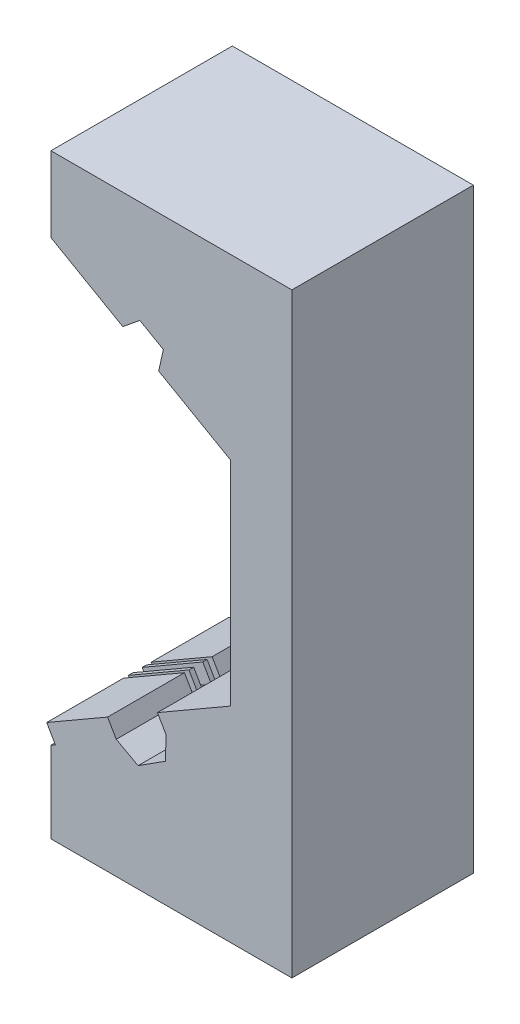
SolidWorks part; units mm, degrees
ref_plane "Front Plane" through (0, 0, 0) normal (0, 0, 1) x (1, 0, 0)
ref_plane "Top Plane" through (0, 0, 0) normal (0, 1, 0) x (1, 0, 0)
ref_plane "Right Plane" through (0, 0, 0) normal (1, 0, 0) x (0, 0, -1)
sketch "Sketch1" plane through (0, 0, 0) normal (0, 0, 1) x (1, 0, 0)
  line L0 (0.7953, -25.456) -> (8.3551, -21.0913)
  line L1 (0.7953, 34.1378) -> (28.6941, 34.1378)
  line L2 (0.7953, 34.1378) -> (0.7953, 25.4267)
  line L3 (0.7953, -34.8515) -> (28.6941, -34.8515)
  line L4 (28.6941, 34.1378) -> (28.6941, -34.8515)
  line L5 (8.3551, -21.0913) -> (10.8905, -22.4625)
  line L6 (10.8905, -22.4625) -> (14.0441, -20.4464)
  line L7 (14.0441, -20.4464) -> (14.1295, -17.7575)
  line L8 (14.1295, -17.7575) -> (22.4796, -12.9365)
  line L11 (22.4796, 13.0123) -> (13.2673, 18.2864)
  line L12 (13.2673, 18.2864) -> (13.8114, 20.7132)
  line L13 (13.8114, 20.7132) -> (11.0901, 22.2712)
  line L14 (11.0901, 22.2712) -> (9.1144, 20.6639)
  line L15 (9.1144, 20.6639) -> (0.7953, 25.4267)
  line L16 (0.7953, -25.456) -> (0.7953, -34.8515)
  line L17 (22.4796, -12.9365) -> (22.4796, -1.5436)
  line L18 (22.4796, -1.5436) -> (23.0165, -1.5436)
  line L20 (24.1482, -0.9477) -> (24.1482, 0.9797)
  line L22 (23.0165, 1.4917) -> (22.4796, 1.4917)
  line L23 (22.4796, 1.4917) -> (22.4796, 13.0123)
  line L24 (0.0371, 25.9047) -> (9.9572, 20.1774) construction
  line L25 (23.0165, -1.5436) -> (23.0165, -1.3275)
  line L26 (23.0165, -1.3275) -> (23.5495, -1.3275)
  line L27 (23.5495, -1.3275) -> (24.1482, -0.9477)
  line L28 (23.0165, 1.4917) -> (23.0165, 1.2788)
  line L29 (23.0165, 1.2788) -> (23.5495, 1.2788)
  line L30 (23.5495, 1.2788) -> (24.1482, 0.9797)
  point P11 (7.6664, 20.3453)
  point P12 (9.1144, 20.6639)
  point P25 (6.6681, 20.9216)
  point P29 (0, 0)
  point P32 (10.8905, 22.1088)
extrude "Boss-Extrude1" add sketch "Sketch1" along normal blind 10 and the other way blind 11
sketch "Sketch2" plane through (22.4796, 0, 0) normal (-1, 0, 0) x (0, 0, 1)
  line L1 (-1.05, -15.5034) -> (-1.55, -15.5034)
  line L2 (-1.05, -15.5034) -> (-1.05, 18.2864)
  line L3 (-1.05, 18.2864) -> (-1.55, 18.2864)
  line L4 (-11, -15.5034) -> (-11, 18.2864)
  line L5 (-2.1, 18.2864) -> (-11, 18.2864)
  line L6 (1.1, 18.2864) -> (10, 18.2864)
  line L7 (0.05, -15.4238) -> (0.55, -15.4238)
  line L8 (0.05, -15.4238) -> (0.05, 18.2864)
  line L9 (0.05, 18.2864) -> (0.55, 18.2864)
  line L10 (10, -15.4238) -> (10, 18.2864)
  line L11 (-1, -12.9523) -> (-1, -1.4976) construction
  line L13 (0.55, -15.4238) -> (0.55, 18.2864)
  line L15 (1.1, -15.4238) -> (1.1, 18.2864)
  line L17 (-1.55, 18.2864) -> (-1.55, -15.5034)
  line L19 (-2.1, 18.2864) -> (-2.1, -15.5034)
  line L20 (0, -12.9523) -> (0, -1.4976) construction
  line L21 (-2.1, -15.5034) -> (-11, -15.5034)
  line L22 (1.1, -15.4238) -> (10, -15.4238)
  dimension "D1" = 0.55
  dimension "D2" = 0.55
  dimension "D3" = 0.05
  dimension "D4" = 0.05
  dimension "D5" = 0.5
  dimension "D6" = 0.5
extrude "Boss-Extrude2" add sketch "Sketch2" along normal blind 0.9
sketch "Sketch4" plane through (21.5796, 0, 0) normal (-1, 0, 0) x (0, 0, 1)
  line L1 (-2.1, 1.4917) -> (1.1, 1.4917)
  line L2 (-2.1, 1.4917) -> (-2.1, -1.5436)
  line L3 (-2.1, -1.5436) -> (1.1, -1.5436)
  line L4 (1.1, 1.4917) -> (1.1, -1.5436)
extrude "Cut-Extrude1" cut sketch "Sketch4" against normal blind 0.9
sketch "Sketch5" plane through (21.5796, 0, 0) normal (-1, 0, 0) x (0, 0, 1)
  line L0 (1.1, 13.5276) -> (1.1, -13.4562) construction
  line L1 (1.1, 2.605) -> (10, 2.605)
  line L2 (1.1, 2.605) -> (1.1, -3.3199)
  line L3 (1.1, -3.3199) -> (10, -3.3199)
  line L4 (10, 2.605) -> (10, -3.3199)
  line L5 (10, -13.4562) -> (10, 13.5276) construction
  line L6 (-11, 13.5276) -> (-11, -13.4562) construction
  line L7 (-11, -4.75) -> (-2.1, -4.75)
  line L8 (-11, -4.75) -> (-11, 3.5097)
  line L9 (-11, 3.5097) -> (-2.1, 3.5097)
  line L10 (-2.1, -4.75) -> (-2.1, 3.5097)
  line L11 (-2.1, -13.4562) -> (-2.1, 13.5276) construction
extrude "Boss-Extrude3" add sketch "Sketch5" against normal blind 3.9
sketch "Sketch6" plane through (11.2216, -19.4364, 0) normal (-0.5, 0.866, 0) x (0.866, 0.5, 0)
  line L0 (-1.4702, 0) -> (-12.9202, 0) construction
  line L1 (13.4092, -10) -> (3.3578, -10)
  line L2 (13.4092, -10) -> (13.4092, -1.1)
  line L3 (13.4092, 11) -> (3.3578, 11)
  line L4 (-11.4513, -10) -> (-11.4513, -1.1)
  line L5 (13.4092, -1.1) -> (3.3578, -1.1)
  line L7 (13.4092, -0.55) -> (3.3855, -0.55)
  line L9 (13.4092, 1.05) -> (3.3855, 1.05)
  line L11 (13.4092, 0) -> (3.3855, 0)
  line L13 (13.4092, 2.1) -> (3.3578, 2.1)
  line L15 (13.4092, 1.55) -> (3.3855, 1.55)
  line L17 (-3.3455, -0.55) -> (-3.3455, 0)
  line L18 (3.3855, 1.55) -> (3.3855, 1.05)
  line L19 (13.4092, -0.55) -> (13.4092, 0)
  line L20 (-11.4513, -0.55) -> (-11.4513, 0)
  line L21 (13.4092, 1.05) -> (13.4092, 1.55)
  line L22 (-11.4513, 1.05) -> (-11.4513, 1.55)
  line L23 (-11.4513, 2.1) -> (-11.4513, 11)
  line L24 (13.4092, 2.1) -> (13.4092, 11)
  line L25 (-3.3455, 1.55) -> (-11.4513, 1.55)
  line L26 (-3.3455, 1.05) -> (-11.4513, 1.05)
  line L27 (-3.3455, 0) -> (-11.4513, 0)
  line L28 (-3.3455, -0.55) -> (-11.4513, -0.55)
  line L29 (-3.3455, 1.05) -> (-3.3455, 1.55)
  line L30 (3.3855, 0) -> (3.3855, -0.55)
  line L31 (-3.31, -10) -> (-3.31, -1.1)
  line L32 (-3.31, 11) -> (-3.31, -10) construction
  line L33 (3.3578, -10) -> (3.3578, -1.1)
  line L34 (3.3578, 11) -> (3.3578, -10) construction
  line L35 (3.3578, 11) -> (3.3578, 2.1)
  line L36 (-3.31, 11) -> (-3.31, 2.1)
  line L37 (-3.31, 11) -> (-11.4513, 11)
  line L38 (-3.31, 2.1) -> (-11.4513, 2.1)
  line L39 (-3.31, -1.1) -> (-11.4513, -1.1)
  line L40 (-3.31, -10) -> (-11.4513, -10)
  dimension "D1" = 1.05
  dimension "D2" = 0.55
  dimension "D3" = 0.55
  dimension "D4" = 0.5
  dimension "D5" = 0.55
extrude "Boss-Extrude4" add sketch "Sketch6" along normal blind 2
